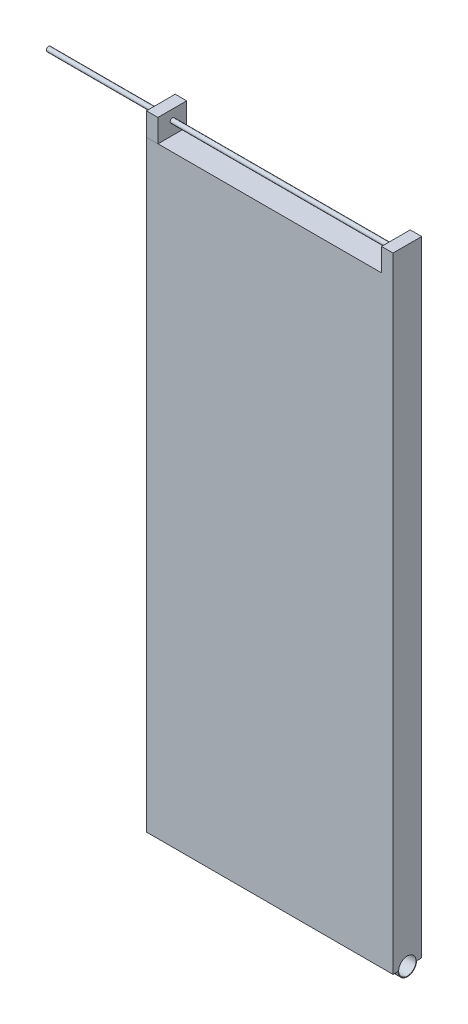
SolidWorks part; units mm, degrees
ref_plane "Plan de face" through (0, 0, 0) normal (0, 0, 1) x (1, 0, 0)
ref_plane "Plan de dessus" through (0, 0, 0) normal (0, 1, 0) x (1, 0, 0)
ref_plane "Plan de droite" through (0, 0, 0) normal (1, 0, 0) x (0, 0, -1)
sketch "Esquisse1" plane through (0, 0, 0) normal (1, 0, 0) x (0, 0, -1)
  line L1 (-6.25, -131.25) -> (6.25, -131.25)
  line L2 (-6.25, -131.25) -> (-6.25, 131.25)
  line L3 (-6.25, 131.25) -> (6.25, 131.25)
  line L4 (6.25, -131.25) -> (6.25, 131.25)
  line L5 (-6.25, -131.25) -> (6.25, 131.25) construction
  line L6 (-6.25, 131.25) -> (6.25, -131.25) construction
  point P0 (0, 0)
  dimension "D1" = 262.5
  dimension "D2" = 12.5
extrude "Boss.-Extru.1" add sketch "Esquisse1" along normal blind 107.5
ref_plane "Plan1" through (107.5, -131.25, 6.25) normal (0, 0, -1) x (-1, 0, 0)
ref_plane "Plan2" through (107.5, -131.25, 6.25) normal (0, 0, -1) x (-1, 0, 0)
sketch "Esquisse5" plane through (107.5, 0, 0) normal (1, 0, 0) x (0, 0, -1)
  line L0 (-6.25, -131.25) -> (6.25, -131.25) construction
  circle A0 centre (0, -131.25) radius 4
extrude "Boss.-Extru.2" add sketch "Esquisse5" against normal blind 107.5 contours A0
sketch "Esquisse6" plane through (107.5, 0, 0) normal (1, 0, 0) x (0, 0, -1)
  circle A0 centre (0, -131.1792) radius 3.8
extrude "Enlèv. mat.-Extru.1" cut sketch "Esquisse6" against normal blind 108.5
sketch "Esquisse8" plane through (0, 131.25, 0) normal (0, 1, 0) x (1, 0, 0)
  line L0 (0, 6.25) -> (5, 6.25)
  line L1 (0, 6.25) -> (0, -6.3028)
  line L2 (5, 6.25) -> (5, -6.3028)
  line L3 (0, -6.3028) -> (5, -6.3028)
  line L4 (107.5, 6.25) -> (0, 6.25) construction
  dimension "D1" = 5
extrude "Boss.-Extru.3" add sketch "Esquisse8" along normal blind 10
sketch "Esquisse9" plane through (0, 131.25, 0) normal (0, 1, 0) x (1, 0, 0)
  line L0 (107.5, 6.25) -> (107.5, -6.25)
  line L1 (107.5, 6.25) -> (102.5, 6.25)
  line L2 (107.5, -6.25) -> (102.5, -6.25)
  line L3 (102.5, 6.25) -> (102.5, -6.25)
  dimension "D1" = 5
extrude "Boss.-Extru.4" add sketch "Esquisse9" along normal blind 10
sketch "Esquisse12" plane through (5, 0, 0) normal (1, 0, 0) x (0, 0, -1)
  line L0 (6.25, 141.25) -> (6.25, 131.25) construction
  circle A0 centre (0.03, 136.9447) radius 1
  point P4 (1.25, 136.9447)
  point P5 (0, 0)
  point P6 (0, 0)
  dimension "D1" = 6.22
extrude "Boss.-Extru.5" add sketch "Esquisse12" along normal blind 101 and the other way blind 54
